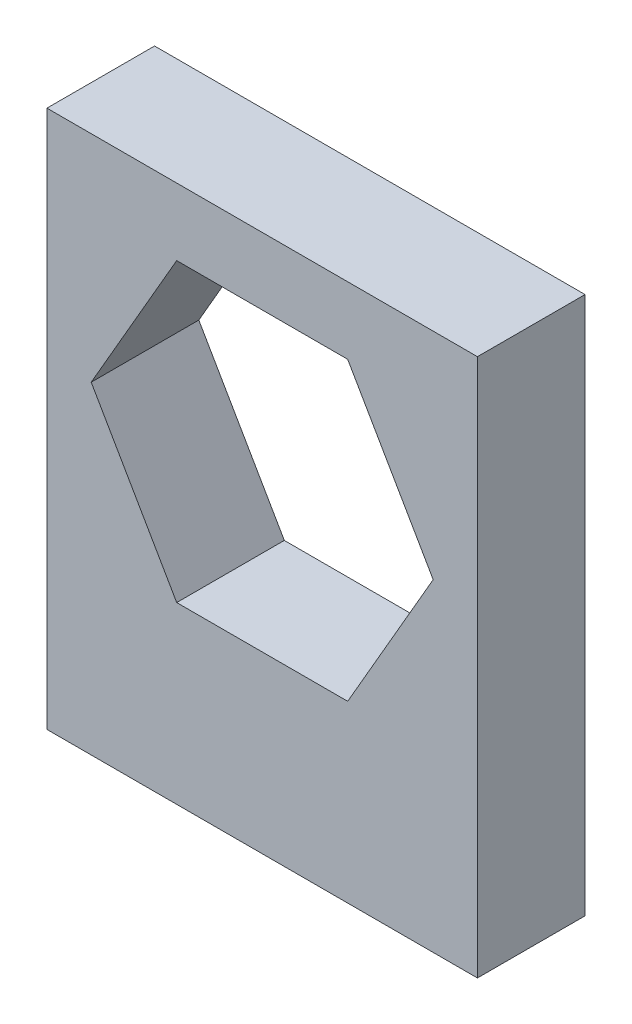
SolidWorks part; units mm, degrees
ref_plane "Front Plane" through (0, 0, 0) normal (0, 0, 1) x (1, 0, 0)
ref_plane "Top Plane" through (0, 0, 0) normal (0, 1, 0) x (1, 0, 0)
ref_plane "Right Plane" through (0, 0, 0) normal (1, 0, 0) x (0, 0, -1)
sketch "Sketch1" plane through (0, 0, 0) normal (0, 0, 1) x (1, 0, 0)
  line L1 (2.5223, 4.3688) -> (-2.5223, 4.3688)
  line L2 (-2.5223, 4.3688) -> (-5.0447, 0)
  line L3 (-5.0447, 0) -> (-2.5223, -4.3688)
  line L4 (-2.5223, -4.3688) -> (2.5223, -4.3688)
  line L5 (2.5223, -4.3688) -> (5.0447, 0)
  line L6 (5.0447, 0) -> (2.5223, 4.3688)
  line L7 (-6.35, 6.35) -> (6.35, 6.35)
  line L8 (-6.35, 6.35) -> (-6.35, -9.525)
  line L9 (-6.35, -9.525) -> (6.35, -9.525)
  line L10 (6.35, 6.35) -> (6.35, -9.525)
  circle A0 centre (0, 0) radius 4.3688 construction
  point P13 (0, 6.35)
  dimension "D1" = 8.7376
  dimension "D2" = 12.7
  dimension "D3" = 15.875
  dimension "D4" = 1.9812
extrude "Boss-Extrude1" add sketch "Sketch1" along normal mid plane 3.175
